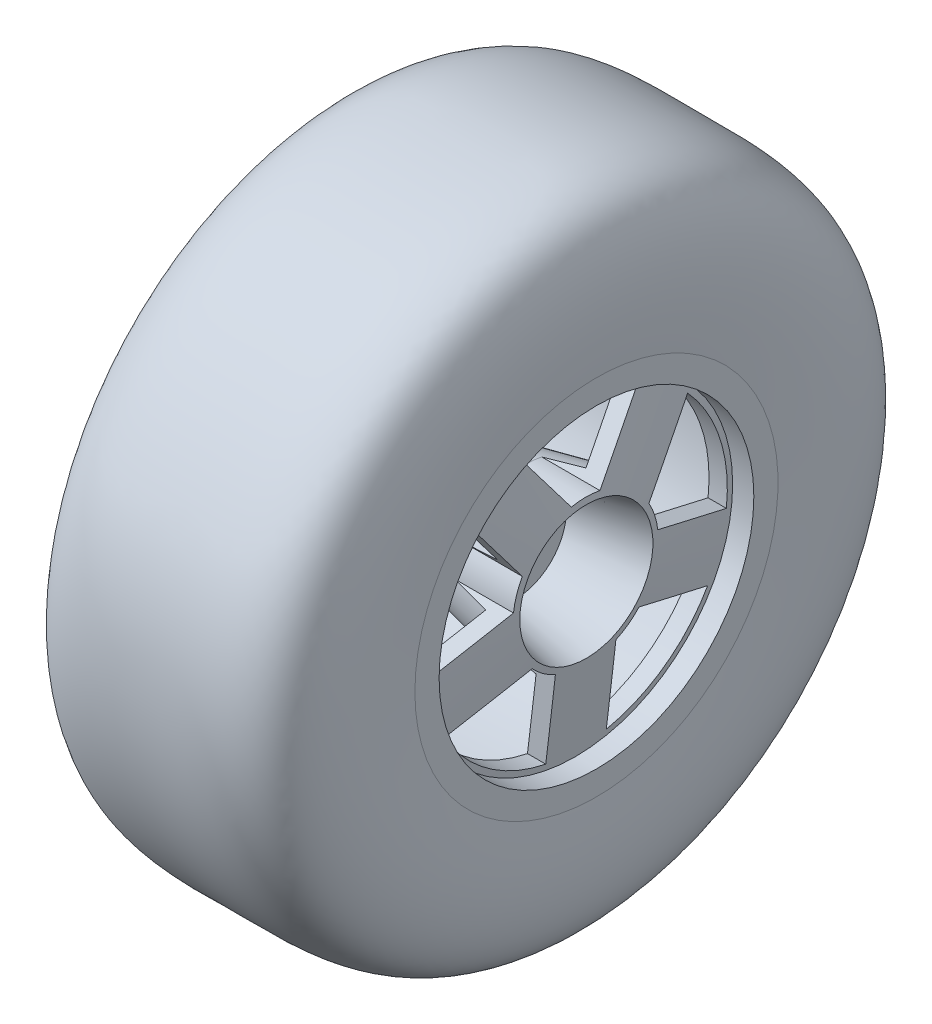
SolidWorks part; units mm, degrees
ref_plane "Front Plane" through (0, 0, 0) normal (0, 0, 1) x (1, 0, 0)
ref_plane "Top Plane" through (0, 0, 0) normal (0, 1, 0) x (1, 0, 0)
ref_plane "Right Plane" through (0, 0, 0) normal (1, 0, 0) x (0, 0, -1)
sketch "Sketch2" plane through (0, 0, 0) normal (0, 0, 1) x (1, 0, 0)
  line L0 (0, 31.7811) -> (0, -27.8084) construction
  line L1 (-63.1838, 0) -> (56.9411, 0) construction
  line L2 (0, 0) -> (0, 9.8717)
  line L3 (0, 9.8717) -> (16.4889, 13.3651)
  line L4 (16.4889, 13.3651) -> (13.847, 35)
  line L5 (13.847, 35) -> (-22.2, 38.5)
  line L6 (-22.2, 38.5) -> (-22.2, 41.8)
  line L7 (-22.2, 41.8) -> (-21.7, 41.8)
  line L8 (0, 0) -> (8, 0)
  line L10 (8, 0) -> (8, 8.5)
  line L11 (8, 8.5) -> (19.8, 11)
  line L12 (19.8, 11) -> (17.9683, 26)
  line L13 (17.9683, 26) -> (21.4683, 26)
  line L14 (21.4683, 26) -> (21.4683, 30)
  spline S0 degree 3 poles (-21.7, 41.8) (-21.5337, 55.2608) (-4.0089, 53.1742) (23.5173, 55.137) (21.9258, 36.0775) (21.4683, 30) knots 0 0 0 0 0.416041 0.696055 1 1 1 1
  point P13 (-16.5286, 52.5408)
  point P16 (17.0966, 50.8803)
  point P20 (21.8261, 35.7884)
  point P21 (19.0423, 50.6079)
  point P22 (0, 0)
  point P24 (-17.8835, 51.4266)
  point P25 (18.7967, 50.4441)
  dimension "D1" = 8
  dimension "D2" = 17
  dimension "D3" = 3
  dimension "D4" = 3
  dimension "D5" = 22
  dimension "D6" = 11.8
  dimension "D7" = 95
  dimension "D8" = 52
  dimension "D9" = 3.5
  dimension "D10" = 4
  dimension "D11" = 77
  dimension "D12" = 70
  dimension "D13" = 42
  dimension "D14" = 0.5
  dimension "D15" = 3.3
  dimension "D16" = 108
revolve "Revolve1" add sketch "Sketch2" angle 360 about L1
sketch "Sketch3" plane through (8, 0, 0) normal (1, 0, 0) x (0, 0, -1)
  circle A0 centre (0, 0) radius 2.15
  dimension "D1" = 4.3
extrude "Cut-Extrude1" cut sketch "Sketch3" against normal up to next
sketch "Sketch4" plane through (21.4683, 0, 0) normal (1, 0, 0) x (0, 0, -1)
  line L0 (-14.6946, 20.2254) -> (0, 0) construction
  line L1 (0, -25) -> (23.7764, -7.7254)
  line L2 (23.7764, -7.7254) -> (14.6946, 20.2254)
  line L3 (14.6946, 20.2254) -> (-14.6946, 20.2254)
  line L4 (-14.6946, 20.2254) -> (-23.7764, -7.7254)
  line L5 (-23.7764, -7.7254) -> (0, -25)
  line L6 (0, 0) -> (14.6946, 20.2254) construction
  line L7 (-23.7764, -7.7254) -> (0, 0) construction
  line L8 (0, -25) -> (0, 0) construction
  line L9 (23.7764, -7.7254) -> (0, 0) construction
  line L10 (-18.7397, 17.2865) -> (-4.0451, -2.9389)
  line L11 (4.0451, -2.9389) -> (18.7397, 17.2865)
  line L12 (25.3215, -2.9701) -> (1.5451, 4.7553)
  line L13 (5, -25) -> (5, 0)
  line L14 (-22.2313, -12.4807) -> (1.5451, -4.7553)
  line L15 (-10.6495, 23.1644) -> (4.0451, 2.9389)
  line L16 (-4.0451, 2.9389) -> (10.6495, 23.1644)
  line L17 (22.2313, -12.4807) -> (-1.5451, -4.7553)
  line L18 (-5, -25) -> (-5, 0)
  line L19 (-25.3215, -2.9701) -> (-1.5451, 4.7553)
  circle A2 centre (0, 0) radius 25
  circle A3 centre (0, 0) radius 25
  circle A4 centre (0, 0) radius 20.2254 construction
  circle A5 centre (0, 0) radius 12
  circle A6 centre (0, 0) radius 12
  dimension "D1" = 1
  dimension "D2" = 1
  dimension "D3" = 5
  dimension "D4" = 5
extrude "Cut-Extrude2" cut sketch "Sketch4" against normal up to next contours L16 A3 L15 L3 | A6 L16 L3 L15 | L12 A3 L11 L2 | A6 L12 L2 L11 | L13 A3 L17 L1 | A6 L13 L1 L17 | L14 A3 L18 L5 | A6 L14 L5 L18 | L10 A3 L19 L4 | A6 L10 L4 L19
sketch "Sketch5" plane through (0, 0, 0) normal (-1, 0, 0) x (0, 0, 1)
  line L1 (0, -6.9282) -> (6, -3.4641)
  line L2 (6, -3.4641) -> (6, 3.4641)
  line L3 (6, 3.4641) -> (0, 6.9282)
  line L4 (0, 6.9282) -> (-6, 3.4641)
  line L5 (-6, 3.4641) -> (-6, -3.4641)
  line L6 (-6, -3.4641) -> (0, -6.9282)
  circle A0 centre (0, 0) radius 6 construction
  dimension "D1" = 12
extrude "Cut-Extrude3" cut sketch "Sketch5" against normal blind 4
